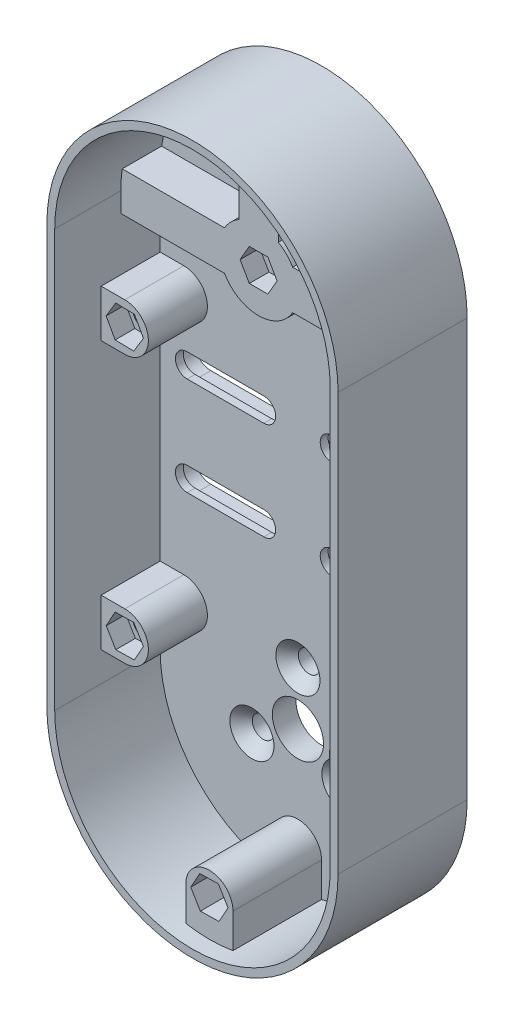
SolidWorks part; units mm, degrees
ref_plane "Alzado" through (0, 0, 0) normal (0, 0, 1) x (1, 0, 0)
ref_plane "Planta" through (0, 0, 0) normal (0, 1, 0) x (1, 0, 0)
ref_plane "Vista lateral" through (0, 0, 0) normal (1, 0, 0) x (0, 0, -1)
sketch "Croquis1" plane through (0, 0, 0) normal (0, 0, 1) x (1, 0, 0)
  line L0 (0, 0) -> (0, 110) construction
  line L1 (-35, 0) -> (35, 0)
  line L2 (-35, 0) -> (-35, 110)
  line L3 (35, 0) -> (35, 110)
  arc A0 (35, 110) -> (-35, 110) centre (0, 110) ccw
  dimension "D3" = 70
  dimension "D1" = 110
  dimension "D2" = 35
extrude "Saliente-Extruir1" add sketch "Croquis1" along normal blind 4
sketch "Croquis2" plane through (0, 0, 4) normal (0, 0, 1) x (1, 0, 0)
  line L0 (0, 110) -> (0, 112.75) construction
  line L1 (0, 110) -> (-5, 110) construction
  line L2 (-8.6603, 105) -> (-35, 105)
  line L3 (0, 110) -> (-5, 110) construction
  line L6 (0, 110) -> (5, 110) construction
  line L7 (0, 110) -> (0, 112.75) construction
  line L12 (0, 110) -> (5, 110) construction
  line L14 (8.6603, 105) -> (35, 105)
  line L15 (-35, 110) -> (-35, 0) construction
  line L16 (35, 0) -> (35, 110) construction
  line L17 (-35, 110) -> (-35, 105)
  line L18 (35, 105) -> (35, 110)
  line L19 (-10, 110) -> (-35, 110) construction
  line L20 (-10, 110) -> (-35, 110) construction
  line L21 (-8.6603, 115) -> (-34.641, 115)
  line L22 (-5, 118.6603) -> (-5, 144.641)
  line L23 (0, 120) -> (0, 145) construction
  line L24 (0, 120) -> (0, 145) construction
  line L25 (5, 118.6603) -> (5, 144.641)
  line L26 (8.6603, 115) -> (34.641, 115)
  line L27 (10, 110) -> (35, 110) construction
  line L28 (10, 110) -> (35, 110) construction
  circle A0 centre (0, 110) radius 2.75
  circle A1 centre (0, 110) radius 10
  arc A2 (35, 110) -> (-35, 110) centre (0, 110) ccw construction
  arc A4 (5, 144.641) -> (-5, 144.641) centre (0, 110) ccw
  arc A6 (-34.641, 115) -> (-35, 110) centre (0, 110) ccw
  arc A9 (35, 110) -> (34.641, 115) centre (0, 110) ccw
  point P3 (-17.5, 110)
  point P11 (0, 127.5)
  point P22 (17.5, 110)
  dimension "D1" = 5.5
  dimension "D3" = 20
extrude "Saliente-Extruir2" add sketch "Croquis2" along normal blind 10
sketch "Croquis3" plane through (0, 0, 0) normal (0, 0, -1) x (-1, 0, 0)
  line L0 (-35, 0) -> (-35, 110) construction
  line L1 (35, 110) -> (35, 0) construction
  line L2 (-35, 0) -> (-35, 110)
  line L3 (-37, 0) -> (-35, 0)
  line L4 (35, 110) -> (35, 0)
  line L5 (35, 0) -> (37, 0)
  line L6 (37, -2) -> (37, 110)
  line L7 (-37, 110) -> (-37, -2)
  line L8 (-37, -2) -> (37, -2)
  line L9 (37, 0) -> (37, 110)
  line L10 (-37, 110) -> (-37, 0)
  arc A0 (35, 110) -> (-35, 110) centre (0, 110) ccw construction
  arc A1 (35, 110) -> (-35, 110) centre (0, 110) ccw
  arc A2 (37, 110) -> (-37, 110) centre (0, 110) ccw
  arc A3 (37, 110) -> (-37, 110) centre (0, 110) ccw
  dimension "D1" = 2
extrude "Saliente-Extruir3" add sketch "Croquis3" against normal blind 30.8
sketch "Croquis4" plane through (0, 0, 4) normal (0, 0, 1) x (1, 0, 0)
  circle A0 centre (0, 110) radius 2.75
extrude "Cortar-Extruir1" cut sketch "Croquis4" against normal up to surface (4 mm away) up to face at (0, 64.25, 0)
hole_wizard "Refrentado para tornillo tapón con cabeza plana de clavija de M52" positions "Croquis3D2" profile "Croquis6" countersink size "M5" standard "Ansi Metric" end condition through all
sketch3d "Croquis3D2"
  line L0 (0, 110, 14) -> (0, 110, 0) construction
  point P0 (0, 110, 0)
sketch "Croquis6" plane through (0, 110, 0) normal (1, 0, 0) x (0, 1, 0)
  line L0 (0, 0) -> (0, 30.8)
  line L1 (0, 30.8) -> (2.75, 30.8)
  line L2 (2.75, 30.8) -> (2.75, 2.85)
  line L3 (2.75, 2.85) -> (5.6, 0)
  line L5 (5.6, 0) -> (0, 0)
  line L6 (-2.75, 2.85) -> (-5.6, 0) construction
  line L11 (0, -6.35) -> (0, 107.95) construction
  dimension "Diámetro de taladro hasta el siguiente" = 5.5
  dimension "Profundidad de taladro hasta el siguiente" = 30.8
  dimension "Diámetro de avellanado cercano" = 11.2
  dimension "Ángulo de avellanado cercano" = 90
sketch "Croquis7" plane through (0, 0, 0) normal (0, 0, -1) x (-1, 0, 0)
  line L1 (2.1893, 105.8349) -> (4.7017, 109.8134)
  line L2 (4.7017, 109.8134) -> (2.5124, 113.9785)
  line L3 (2.5124, 113.9785) -> (-2.1893, 114.1651)
  line L4 (-2.1893, 114.1651) -> (-4.7017, 110.1866)
  line L5 (-4.7017, 110.1866) -> (-2.5124, 106.0215)
  line L6 (-2.5124, 106.0215) -> (2.1893, 105.8349)
  circle A0 centre (0, 110) radius 4.075 construction
  dimension "D1" = 8.15
extrude "Cortar-Extruir2" cut sketch "Croquis7" against normal blind 5
sketch "Croquis8" plane through (0, 0, 14) normal (0, 0, 1) x (1, 0, 0)
  line L1 (4.7054, 110) -> (2.3527, 114.075)
  line L2 (2.3527, 114.075) -> (-2.3527, 114.075)
  line L3 (-2.3527, 114.075) -> (-4.7054, 110)
  line L4 (-4.7054, 110) -> (-2.3527, 105.925)
  line L5 (-2.3527, 105.925) -> (2.3527, 105.925)
  line L6 (2.3527, 105.925) -> (4.7054, 110)
  circle A0 centre (0, 110) radius 4.075 construction
  dimension "D1" = 8.15
extrude "Cortar-Extruir3" cut sketch "Croquis8" against normal blind 5
ref_plane "Plano1" through (0, 5, 0) normal (0, -1, 0) x (-1, 0, 0)
sketch "Croquis16" plane through (0, 0, 4) normal (0, 0, 1) x (1, 0, 0)
  line L0 (-37, 0) -> (-37, 110) construction
  line L1 (-37, 4) -> (37, 4)
  line L2 (-37, 4) -> (-37, 0)
  line L3 (-37, 0) -> (37, 0)
  line L4 (37, 4) -> (37, 0)
extrude "Cortar-Extruir5" cut sketch "Croquis16" against normal mid plane 70
sketch "Croquis15" plane through (0, 0, 4) normal (0, 0, 1) x (1, 0, 0)
  line L0 (0, 110) -> (0, 4)
  line L1 (0, 4) -> (-35, 4)
  line L2 (-35, 105) -> (-35, 4) construction
  line L3 (0, 4) -> (35, 4)
  line L4 (35, 4) -> (35, 105) construction
  arc A0 (-35, 4) -> (35, 4) centre (0, 4) ccw
  dimension "D2" = 35
  dimension "D1" = 106
extrude "Saliente-Extruir4" add sketch "Croquis15" against normal blind 4
sketch "Croquis17" plane through (0, 0, 4) normal (0, 0, 1) x (1, 0, 0)
  line L0 (-37, 4) -> (-35, 4)
  line L1 (35, 4) -> (37, 4)
  arc A0 (-35, 4) -> (35, 4) centre (0, 4) ccw construction
  arc A1 (-35, 4) -> (35, 4) centre (0, 4) ccw
  arc A2 (-37, 4) -> (37, 4) centre (0, 4) ccw
  dimension "D1" = 2
extrude "Saliente-Extruir5" add sketch "Croquis17" against normal blind 4
sketch "Croquis18" plane through (0, 0, 4) normal (0, 0, 1) x (1, 0, 0)
  line L0 (-37, 4) -> (-35, 4)
  line L1 (35, 4) -> (37, 4)
  arc A0 (-37, 4) -> (37, 4) centre (0, 4) ccw construction
  arc A1 (-37, 4) -> (37, 4) centre (0, 4) ccw
  arc A2 (-35, 4) -> (35, 4) centre (0, 4) ccw
  dimension "D1" = 2
extrude "Saliente-Extruir6" add sketch "Croquis18" along normal blind 26.8
sketch "Croquis19" plane through (0, 0, 4) normal (0, 0, 1) x (1, 0, 0)
  line L0 (0, 110) -> (0, 4)
  circle A0 centre (0, 4) radius 6
  circle A1 centre (0, 4) radius 13.5
  circle A2 centre (0, 4) radius 6.5
  dimension "D2" = 12
  dimension "D3" = 27
  dimension "D4" = 13
  dimension "D1" = 106
sketch "Croquis20" plane through (0, 0, 4) normal (0, 0, 1) x (1, 0, 0)
  line L0 (0, 110) -> (0, 4) construction
  circle A0 centre (0, 17.5) radius 2.8
  circle A1 centre (0, 4) radius 13.5 construction
  circle A2 centre (11.6913, -2.75) radius 2.8
  circle A3 centre (-11.6913, -2.75) radius 2.8
  point P12 (0, 4)
  dimension "D1" = 5.6
  dimension "D2" = 3
hole_wizard "Refrentado para tornillo tapón con cabeza plana de clavija de M53" positions "Croquis22" profile "Croquis21" countersink size "M5" standard "Ansi Metric" end condition through all
sketch "Croquis22" plane through (0, 0, 4) normal (0, 0, 1) x (1, 0, 0)
  point P0 (0, 17.5)
  point P3 (-11.6913, -2.75)
  point P6 (11.6913, -2.75)
sketch "Croquis21" plane through (0, 17.5, 4) normal (1, 0, 0) x (0, -1, 0)
  line L0 (0, 0) -> (0, 4)
  line L1 (0, 4) -> (2.75, 4)
  line L2 (2.75, 4) -> (2.75, 2.85)
  line L3 (2.75, 2.85) -> (5.6, 0)
  line L5 (5.6, 0) -> (0, 0)
  line L6 (-2.75, 2.85) -> (-5.6, 0) construction
  line L11 (0, -6.35) -> (0, 107.95) construction
  dimension "Diámetro de taladro hasta el siguiente" = 5.5
  dimension "Profundidad de taladro hasta el siguiente" = 4
  dimension "Diámetro de avellanado cercano" = 11.2
  dimension "Ángulo de avellanado cercano" = 90
extrude "Cortar-Extruir6" cut sketch "Croquis19" against normal blind 10 contours A2
sketch "Croquis23" plane through (0, 0, 4) normal (0, 0, 1) x (1, 0, 0)
  line L0 (0, 110) -> (0, 4) construction
  line L1 (-28.1376, 70) -> (-8.6603, 70) construction
  line L2 (-28.1376, 73) -> (-8.6603, 73)
  line L3 (-28.1376, 67) -> (-8.6603, 67)
  line L5 (28.1376, 70) -> (8.6603, 70) construction
  line L6 (28.1376, 73) -> (8.6603, 73)
  line L7 (28.1376, 67) -> (8.6603, 67)
  line L8 (28.1376, 45) -> (8.6603, 45) construction
  line L9 (28.1376, 42) -> (8.6603, 42)
  line L10 (28.1376, 48) -> (8.6603, 48)
  line L11 (-28.1376, 45) -> (-8.6603, 45) construction
  line L12 (-28.1376, 42) -> (-8.6603, 42)
  line L13 (-28.1376, 48) -> (-8.6603, 48)
  line L14 (-8.6603, 105) -> (-35, 105) construction
  arc A0 (-28.1376, 73) -> (-28.1376, 67) centre (-28.1376, 70) ccw
  arc A1 (-8.6603, 67) -> (-8.6603, 73) centre (-8.6603, 70) ccw
  arc A2 (28.1376, 73) -> (28.1376, 67) centre (28.1376, 70) cw
  arc A3 (8.6603, 67) -> (8.6603, 73) centre (8.6603, 70) cw
  arc A4 (28.1376, 42) -> (28.1376, 48) centre (28.1376, 45) ccw
  arc A5 (8.6603, 48) -> (8.6603, 42) centre (8.6603, 45) ccw
  arc A6 (-28.1376, 42) -> (-28.1376, 48) centre (-28.1376, 45) cw
  arc A7 (-8.6603, 48) -> (-8.6603, 42) centre (-8.6603, 45) cw
  point P6 (-18.3989, 70)
  point P15 (18.3989, 70)
  point P22 (18.3989, 45)
  point P29 (-18.3989, 45)
  dimension "D1" = 3
  dimension "D3" = 3
  dimension "D6" = 3
  dimension "D2" = 25
  dimension "D4" = 35
  dimension "D5" = 25
extrude "Cortar-Extruir7" cut sketch "Croquis23" against normal blind 10
sketch "Croquis26" plane through (0, 0, 4) normal (0, 0, 1) x (1, 0, 0)
  line L0 (0, -31) -> (0, -21.7835) construction
  line L1 (-6, -30.4819) -> (-6, -21.7835)
  line L2 (6, -30.4819) -> (6, -21.7835)
  line L4 (2.4438, -25.8382) -> (4.7334, -21.6944)
  line L5 (4.7334, -21.6944) -> (2.2896, -17.6397)
  line L6 (2.2896, -17.6397) -> (-2.4438, -17.7287)
  line L7 (-2.4438, -17.7287) -> (-4.7334, -21.8725)
  line L8 (-4.7334, -21.8725) -> (-2.2896, -25.9273)
  line L9 (-2.2896, -25.9273) -> (2.4438, -25.8382)
  arc A0 (-35, 4) -> (35, 4) centre (0, 4) ccw construction
  arc A2 (6, -21.7835) -> (-6, -21.7835) centre (0, -21.7835) ccw
  circle A3 centre (0, -21.7835) radius 4.1 construction
  arc A4 (-6, -30.4819) -> (6, -30.4819) centre (0, 4) ccw
  point P6 (0, -26.3917)
  dimension "D1" = 6
  dimension "D2" = 8.2
extrude "Saliente-Extruir7" add sketch "Croquis26" along normal blind 22.5
sketch "Croquis27" plane through (0, 0, 4) normal (0, 0, 1) x (1, 0, 0)
  line L0 (-4.7334, -21.8725) -> (-2.2896, -25.9273) construction
  line L1 (-2.2896, -25.9273) -> (2.4438, -25.8382) construction
  line L2 (2.4438, -25.8382) -> (4.7334, -21.6944) construction
  line L3 (4.7334, -21.6944) -> (2.2896, -17.6397) construction
  line L4 (2.2896, -17.6397) -> (-2.4438, -17.7287) construction
  line L5 (-2.4438, -17.7287) -> (-4.7334, -21.8725) construction
  line L6 (-4.7334, -21.8725) -> (-2.2896, -25.9273)
  line L7 (-2.2896, -25.9273) -> (2.4438, -25.8382)
  line L8 (2.4438, -25.8382) -> (4.7334, -21.6944)
  line L9 (4.7334, -21.6944) -> (2.2896, -17.6397)
  line L10 (2.2896, -17.6397) -> (-2.4438, -17.7287)
  line L11 (-2.4438, -17.7287) -> (-4.7334, -21.8725)
  line L12 (-1.1727, -23.9059) -> (1.2517, -23.8603)
  line L13 (1.2517, -23.8603) -> (2.4244, -21.7379)
  line L14 (2.4244, -21.7379) -> (1.1727, -19.661)
  line L15 (1.1727, -19.661) -> (-1.2517, -19.7067)
  line L16 (-1.2517, -19.7067) -> (-2.4244, -21.8291)
  line L17 (-2.4244, -21.8291) -> (-1.1727, -23.9059)
  dimension "D1" = 2
extrude "Saliente-Extruir8" add sketch "Croquis27" along normal blind 15
sketch "Croquis28" plane through (0, 0, 19) normal (0, 0, 1) x (1, 0, 0)
  line L0 (-1.2517, -19.7067) -> (1.2517, -23.8603) construction
  circle A0 centre (0, -21.7835) radius 3
  dimension "D1" = 6
extrude "Cortar-Extruir9" cut sketch "Croquis28" against normal blind 15
sketch "Croquis29" plane through (0, 0, 4) normal (0, 0, 1) x (1, 0, 0)
  line L0 (0, 110) -> (0, -21.7835) construction
  line L1 (-35, 105) -> (-35, 4) construction
  line L2 (-35, 110) -> (-35, 4) construction
  line L3 (-35, 17.5) -> (-29, 17.5) construction
  line L4 (-35, 23.5) -> (-29, 23.5)
  line L5 (-35, 11.5) -> (-29, 11.5)
  line L6 (-35, 23.5) -> (-35, 11.5)
  line L8 (-31.2865, 13.3545) -> (-26.5532, 13.4471)
  line L9 (-26.5532, 13.4471) -> (-24.2666, 17.5926)
  line L10 (-24.2666, 17.5926) -> (-26.7135, 21.6455)
  line L11 (-26.7135, 21.6455) -> (-31.4468, 21.5529)
  line L12 (-31.4468, 21.5529) -> (-33.7334, 17.4074)
  line L13 (-33.7334, 17.4074) -> (-31.2865, 13.3545)
  line L17 (35, 23.5) -> (35, 11.5)
  line L18 (35, 17.5) -> (29, 17.5) construction
  line L19 (33.7334, 17.4074) -> (31.2865, 13.3545)
  line L20 (31.4468, 21.5529) -> (33.7334, 17.4074)
  line L21 (26.7135, 21.6455) -> (31.4468, 21.5529)
  line L22 (24.2666, 17.5926) -> (26.7135, 21.6455)
  line L23 (26.5532, 13.4471) -> (24.2666, 17.5926)
  line L24 (31.2865, 13.3545) -> (26.5532, 13.4471)
  line L25 (35, 11.5) -> (29, 11.5)
  line L26 (35, 23.5) -> (29, 23.5)
  line L27 (-35, 51.5) -> (35, 51.5) construction
  line L29 (35, 79.5) -> (35, 91.5)
  line L30 (35, 85.5) -> (29, 85.5) construction
  line L31 (35, 79.5) -> (29, 79.5)
  line L32 (35, 91.5) -> (29, 91.5)
  line L33 (31.2865, 89.6455) -> (26.5532, 89.5529)
  line L34 (26.5532, 89.5529) -> (24.2666, 85.4074)
  line L35 (24.2666, 85.4074) -> (26.7135, 81.3545)
  line L36 (26.7135, 81.3545) -> (31.4468, 81.4471)
  line L37 (31.4468, 81.4471) -> (33.7334, 85.5926)
  line L38 (33.7334, 85.5926) -> (31.2865, 89.6455)
  line L39 (-35, 79.5) -> (-35, 91.5)
  line L40 (-35, 85.5) -> (-29, 85.5) construction
  line L41 (-33.7334, 85.5926) -> (-31.2865, 89.6455)
  line L42 (-31.4468, 81.4471) -> (-33.7334, 85.5926)
  line L43 (-26.7135, 81.3545) -> (-31.4468, 81.4471)
  line L44 (-24.2666, 85.4074) -> (-26.7135, 81.3545)
  line L45 (-26.5532, 89.5529) -> (-24.2666, 85.4074)
  line L46 (-31.2865, 89.6455) -> (-26.5532, 89.5529)
  line L47 (-35, 91.5) -> (-29, 91.5)
  line L48 (-35, 79.5) -> (-29, 79.5)
  circle A3 centre (-29, 17.5) radius 4.1 construction
  arc A4 (-29, 11.5) -> (-29, 23.5) centre (-29, 17.5) ccw
  circle A5 centre (29, 17.5) radius 4.1 construction
  arc A6 (29, 11.5) -> (29, 23.5) centre (29, 17.5) cw
  circle A7 centre (29, 85.5) radius 4.1 construction
  arc A8 (29, 91.5) -> (29, 79.5) centre (29, 85.5) ccw
  circle A9 centre (-29, 85.5) radius 4.1 construction
  arc A10 (-29, 91.5) -> (-29, 79.5) centre (-29, 85.5) cw
  point P6 (-30.39, 17.5)
  point P78 (-30.39, 85.5)
  dimension "D2" = 6
  dimension "D1" = 6
  dimension "D3" = 8.2
  dimension "D5" = 28
  dimension "D6" = 6
extrude "Saliente-Extruir9" add sketch "Croquis29" along normal blind 15
sketch "Croquis30" plane through (0, 0, 4) normal (0, 0, 1) x (1, 0, 0)
  line L0 (-31.4244, 17.4526) -> (-30.1712, 15.3767)
  line L1 (-30.1712, 15.3767) -> (-27.7467, 15.4241)
  line L2 (-27.7467, 15.4241) -> (-26.5756, 17.5474)
  line L3 (-26.5756, 17.5474) -> (-27.8288, 19.6233)
  line L4 (-27.8288, 19.6233) -> (-30.2533, 19.5759)
  line L5 (-30.2533, 19.5759) -> (-31.4244, 17.4526)
  line L6 (-33.7334, 17.4074) -> (-31.2865, 13.3545)
  line L7 (-31.2865, 13.3545) -> (-26.5532, 13.4471)
  line L8 (-26.5532, 13.4471) -> (-24.2666, 17.5926)
  line L9 (-24.2666, 17.5926) -> (-26.7135, 21.6455)
  line L10 (-26.7135, 21.6455) -> (-31.4468, 21.5529)
  line L11 (-31.4468, 21.5529) -> (-33.7334, 17.4074)
  line L12 (-33.7334, 17.4074) -> (-31.2865, 13.3545)
  line L13 (-31.2865, 13.3545) -> (-26.5532, 13.4471)
  line L14 (-26.5532, 13.4471) -> (-24.2666, 17.5926)
  line L15 (-24.2666, 17.5926) -> (-26.7135, 21.6455)
  line L16 (-26.7135, 21.6455) -> (-31.4468, 21.5529)
  line L17 (-31.4468, 21.5529) -> (-33.7334, 17.4074)
  line L18 (0, 110) -> (0, -21.7835) construction
  line L19 (-35, 51.5) -> (35, 51.5) construction
  line L23 (27.7467, 15.4241) -> (26.5756, 17.5474)
  line L24 (26.5756, 17.5474) -> (27.8288, 19.6233)
  line L25 (27.8288, 19.6233) -> (30.2533, 19.5759)
  line L26 (30.2533, 19.5759) -> (31.4244, 17.4526)
  line L27 (31.4244, 17.4526) -> (30.1712, 15.3767)
  line L28 (30.1712, 15.3767) -> (27.7467, 15.4241)
  line L29 (31.2865, 13.3545) -> (26.5532, 13.4471)
  line L30 (26.5532, 13.4471) -> (24.2666, 17.5926)
  line L31 (24.2666, 17.5926) -> (26.7135, 21.6455)
  line L32 (26.7135, 21.6455) -> (31.4468, 21.5529)
  line L33 (31.4468, 21.5529) -> (33.7334, 17.4074)
  line L34 (33.7334, 17.4074) -> (31.2865, 13.3545)
  line L35 (-35, 79.5) -> (-35, 23.5) construction
  line L36 (35, 23.5) -> (35, 79.5) construction
  line L37 (-26.5532, 89.5529) -> (-24.2666, 85.4074)
  line L38 (-24.2666, 85.4074) -> (-26.7135, 81.3545)
  line L39 (-31.4468, 81.4471) -> (-33.7334, 85.5926)
  line L40 (-33.7334, 85.5926) -> (-31.2865, 89.6455)
  line L41 (-26.7135, 81.3545) -> (-31.4468, 81.4471)
  line L42 (-31.2865, 89.6455) -> (-26.5532, 89.5529)
  line L43 (-30.2533, 83.4241) -> (-31.4244, 85.5474)
  line L44 (-27.8288, 83.3767) -> (-30.2533, 83.4241)
  line L45 (-26.5756, 85.4526) -> (-27.8288, 83.3767)
  line L46 (-27.7467, 87.5759) -> (-26.5756, 85.4526)
  line L47 (-30.1712, 87.6233) -> (-27.7467, 87.5759)
  line L48 (-31.4244, 85.5474) -> (-30.1712, 87.6233)
  line L49 (31.2865, 89.6455) -> (26.5532, 89.5529)
  line L50 (26.7135, 81.3545) -> (31.4468, 81.4471)
  line L51 (31.4244, 85.5474) -> (30.1712, 87.6233)
  line L52 (30.1712, 87.6233) -> (27.7467, 87.5759)
  line L53 (27.7467, 87.5759) -> (26.5756, 85.4526)
  line L54 (26.5756, 85.4526) -> (27.8288, 83.3767)
  line L55 (27.8288, 83.3767) -> (30.2533, 83.4241)
  line L56 (30.2533, 83.4241) -> (31.4244, 85.5474)
  line L57 (33.7334, 85.5926) -> (31.2865, 89.6455)
  line L58 (31.4468, 81.4471) -> (33.7334, 85.5926)
  line L59 (24.2666, 85.4074) -> (26.7135, 81.3545)
  line L60 (26.5532, 89.5529) -> (24.2666, 85.4074)
  dimension "D3" = 28
  dimension "D1" = 0
  dimension "D2" = 2
extrude "Saliente-Extruir10" add sketch "Croquis30" along normal blind 10
sketch "Croquis31" plane through (0, 0, 14) normal (0, 0, 1) x (1, 0, 0)
  line L0 (-30.2533, 19.5759) -> (-27.7467, 15.4241) construction
  line L1 (0, -33) -> (0, 147) construction
  line L2 (-30.1712, 87.6233) -> (-27.8288, 83.3767) construction
  line L3 (27.7467, 87.5759) -> (30.2533, 83.4241) construction
  circle A0 centre (-29, 17.5) radius 3
  arc A1 (-37, 4) -> (37, 4) centre (0, 4) ccw construction
  arc A2 (37, 110) -> (-37, 110) centre (0, 110) ccw construction
  circle A3 centre (29, 17.5) radius 3
  circle A4 centre (-29, 85.5) radius 3
  circle A5 centre (29, 85.5) radius 3
  dimension "D1" = 6
  dimension "D2" = 6
  dimension "D3" = 6
extrude "Cortar-Extruir10" cut sketch "Croquis31" against normal blind 10
sketch "Croquis35" plane through (0, 0, 0) normal (0, 0, -1) x (-1, 0, 0)
  line L0 (-37, 110) -> (-37, 4) construction
  line L1 (37, 4) -> (37, 110) construction
  line L2 (-8.6603, 42) -> (-28.1376, 42) construction
  line L3 (-28.1376, 48) -> (-8.6603, 48) construction
  line L4 (2.1893, 105.8349) -> (4.7017, 109.8134) construction
  line L5 (4.7017, 109.8134) -> (2.5124, 113.9785) construction
  line L6 (-2.1893, 114.1651) -> (2.5124, 113.9785) construction
  line L7 (-2.1893, 114.1651) -> (-4.7017, 110.1866) construction
  line L8 (-4.7017, 110.1866) -> (-2.5124, 106.0215) construction
  line L9 (2.1893, 105.8349) -> (-2.5124, 106.0215) construction
  line L10 (-8.6603, 67) -> (-28.1376, 67) construction
  line L11 (-28.1376, 73) -> (-8.6603, 73) construction
  line L12 (28.1376, 67) -> (8.6603, 67) construction
  line L13 (8.6603, 73) -> (28.1376, 73) construction
  line L14 (8.6603, 48) -> (28.1376, 48) construction
  line L15 (28.1376, 42) -> (8.6603, 42) construction
  line L16 (-37, 110) -> (-37, 4)
  line L17 (37, 4) -> (37, 110)
  line L18 (-8.6603, 42) -> (-28.1376, 42)
  line L19 (-28.1376, 48) -> (-8.6603, 48)
  line L20 (2.1893, 105.8349) -> (4.7017, 109.8134)
  line L21 (4.7017, 109.8134) -> (2.5124, 113.9785)
  line L22 (-2.1893, 114.1651) -> (2.5124, 113.9785)
  line L23 (-2.1893, 114.1651) -> (-4.7017, 110.1866)
  line L24 (-4.7017, 110.1866) -> (-2.5124, 106.0215)
  line L25 (2.1893, 105.8349) -> (-2.5124, 106.0215)
  line L26 (-8.6603, 67) -> (-28.1376, 67)
  line L27 (-28.1376, 73) -> (-8.6603, 73)
  line L28 (28.1376, 67) -> (8.6603, 67)
  line L29 (8.6603, 73) -> (28.1376, 73)
  line L30 (8.6603, 48) -> (28.1376, 48)
  line L31 (28.1376, 42) -> (8.6603, 42)
  arc A0 (-37, 4) -> (37, 4) centre (0, 4) ccw construction
  circle A1 centre (0, 110) radius 2.75
  circle A2 centre (0, 110) radius 2.75
  arc A3 (37, 110) -> (-37, 110) centre (0, 110) ccw construction
  arc A4 (-8.6603, 42) -> (-8.6603, 48) centre (-8.6603, 45) ccw construction
  arc A5 (-28.1376, 48) -> (-28.1376, 42) centre (-28.1376, 45) ccw construction
  circle A6 centre (0, 110) radius 5.6 construction
  arc A7 (-28.1376, 73) -> (-28.1376, 67) centre (-28.1376, 70) ccw construction
  arc A8 (-8.6603, 67) -> (-8.6603, 73) centre (-8.6603, 70) ccw construction
  arc A9 (8.6603, 73) -> (8.6603, 67) centre (8.6603, 70) ccw construction
  arc A10 (28.1376, 67) -> (28.1376, 73) centre (28.1376, 70) ccw construction
  arc A11 (8.6603, 48) -> (8.6603, 42) centre (8.6603, 45) ccw construction
  arc A12 (28.1376, 42) -> (28.1376, 48) centre (28.1376, 45) ccw construction
  circle A13 centre (0, 17.5) radius 2.75 construction
  circle A14 centre (0, 4) radius 6.5 construction
  circle A15 centre (11.6913, -2.75) radius 2.75 construction
  circle A16 centre (-11.6913, -2.75) radius 2.75 construction
  arc A17 (-37, 4) -> (37, 4) centre (0, 4) ccw
  arc A18 (37, 110) -> (-37, 110) centre (0, 110) ccw
  arc A19 (-8.6603, 42) -> (-8.6603, 48) centre (-8.6603, 45) ccw
  arc A20 (-28.1376, 48) -> (-28.1376, 42) centre (-28.1376, 45) ccw
  circle A21 centre (0, 110) radius 5.6
  arc A22 (-28.1376, 73) -> (-28.1376, 67) centre (-28.1376, 70) ccw
  arc A23 (-8.6603, 67) -> (-8.6603, 73) centre (-8.6603, 70) ccw
  arc A24 (8.6603, 73) -> (8.6603, 67) centre (8.6603, 70) ccw
  arc A25 (28.1376, 67) -> (28.1376, 73) centre (28.1376, 70) ccw
  arc A26 (8.6603, 48) -> (8.6603, 42) centre (8.6603, 45) ccw
  arc A27 (28.1376, 42) -> (28.1376, 48) centre (28.1376, 45) ccw
  circle A28 centre (0, 17.5) radius 2.75
  circle A29 centre (0, 4) radius 6.5
  circle A30 centre (11.6913, -2.75) radius 2.75
  circle A31 centre (-11.6913, -2.75) radius 2.75
  line M2 (8.6603, 48) -> (28.1376, 48)
  arc M3 (28.1376, 48) -> (28.1376, 42) centre (28.1376, 45) cw
  line M4 (28.1376, 42) -> (8.6603, 42)
  arc M5 (8.6603, 42) -> (8.6603, 48) centre (8.6603, 45) cw
  line M6 (-8.6603, 42) -> (-28.1376, 42)
  arc M7 (-28.1376, 42) -> (-28.1376, 48) centre (-28.1376, 45) cw
  line M8 (-28.1376, 48) -> (-8.6603, 48)
  arc M9 (-8.6603, 48) -> (-8.6603, 42) centre (-8.6603, 45) cw
  line M10 (-8.6603, 67) -> (-28.1376, 67)
  arc M11 (-28.1376, 67) -> (-28.1376, 73) centre (-28.1376, 70) cw
  line M12 (-28.1376, 73) -> (-8.6603, 73)
  arc M13 (-8.6603, 73) -> (-8.6603, 67) centre (-8.6603, 70) cw
  line M14 (8.6603, 73) -> (28.1376, 73)
  arc M15 (28.1376, 73) -> (28.1376, 67) centre (28.1376, 70) cw
  line M16 (28.1376, 67) -> (8.6603, 67)
  arc M17 (8.6603, 67) -> (8.6603, 73) centre (8.6603, 70) cw
  circle M18 centre (0, 4) radius 6.5
  circle M19 centre (0, 17.5) radius 2.75
  circle M20 centre (11.6913, -2.75) radius 2.75
  circle M21 centre (-11.6913, -2.75) radius 2.75
  arc M22 (-37, 4) -> (37, 4) centre (0, 4) ccw
  line M23 (37, 4) -> (37, 110)
  arc M24 (37, 110) -> (-37, 110) centre (0, 110) ccw
  line M25 (-37, 110) -> (-37, 4)
  circle M26 centre (0, 110) radius 5.6
  dimension "D1" = 0
extrude "Saliente-Extruir11" add sketch "Croquis35" along normal blind 2 contours M25 M22 M23 M24 M9 M6 M7 M8 M17 M14 M15 M16 M19 M21 M26 M20 M18 M13 M10 M11 M12 M5 M2 M3 M4
sketch "Croquis36" plane through (0, 0, -2) normal (0, 0, -1) x (-1, 0, 0)
  line L0 (-28.1376, 73) -> (-28.1376, 67) construction
  line L3 (-28.1376, 70) -> (-8.6603, 70) construction
  line L4 (-28.1376, 74.15) -> (-8.6603, 74.15)
  line L5 (-28.1376, 65.85) -> (-8.6603, 65.85)
  line L6 (0, 107.25) -> (0, -2.5) construction
  line L7 (28.1376, 70) -> (8.6603, 70) construction
  line L8 (28.1376, 74.15) -> (8.6603, 74.15)
  line L9 (28.1376, 65.85) -> (8.6603, 65.85)
  line L10 (-18.3989, 67) -> (-18.3989, 48) construction
  line L13 (-8.6603, 67) -> (-28.1376, 67) construction
  line L14 (-28.1376, 48) -> (-8.6603, 48) construction
  line L15 (-18.3989, 57.5) -> (-10.8781, 57.5) construction
  line L16 (-28.1376, 45) -> (-8.6603, 45) construction
  line L17 (-28.1376, 40.85) -> (-8.6603, 40.85)
  line L18 (-28.1376, 49.15) -> (-8.6603, 49.15)
  line L19 (28.1376, 45) -> (8.6603, 45) construction
  line L20 (28.1376, 40.85) -> (8.6603, 40.85)
  line L21 (28.1376, 49.15) -> (8.6603, 49.15)
  arc A0 (-28.1376, 73) -> (-28.1376, 67) centre (-28.1376, 70) ccw construction
  arc A1 (-28.1376, 74.15) -> (-28.1376, 65.85) centre (-28.1376, 70) ccw
  arc A2 (-8.6603, 65.85) -> (-8.6603, 74.15) centre (-8.6603, 70) ccw
  circle A3 centre (0, 110) radius 2.75 construction
  circle A4 centre (0, 4) radius 6.5 construction
  arc A5 (28.1376, 74.15) -> (28.1376, 65.85) centre (28.1376, 70) cw
  arc A6 (8.6603, 65.85) -> (8.6603, 74.15) centre (8.6603, 70) cw
  arc A7 (-28.1376, 40.85) -> (-28.1376, 49.15) centre (-28.1376, 45) cw
  arc A8 (-8.6603, 49.15) -> (-8.6603, 40.85) centre (-8.6603, 45) cw
  arc A9 (28.1376, 40.85) -> (28.1376, 49.15) centre (28.1376, 45) ccw
  arc A10 (8.6603, 49.15) -> (8.6603, 40.85) centre (8.6603, 45) ccw
  point P9 (-18.3989, 70)
  point P23 (18.3989, 70)
  point P38 (-18.3989, 45)
  point P45 (18.3989, 45)
  dimension "D1" = 4.15
extrude "Cortar-Extruir12" cut sketch "Croquis36" against normal blind 4
